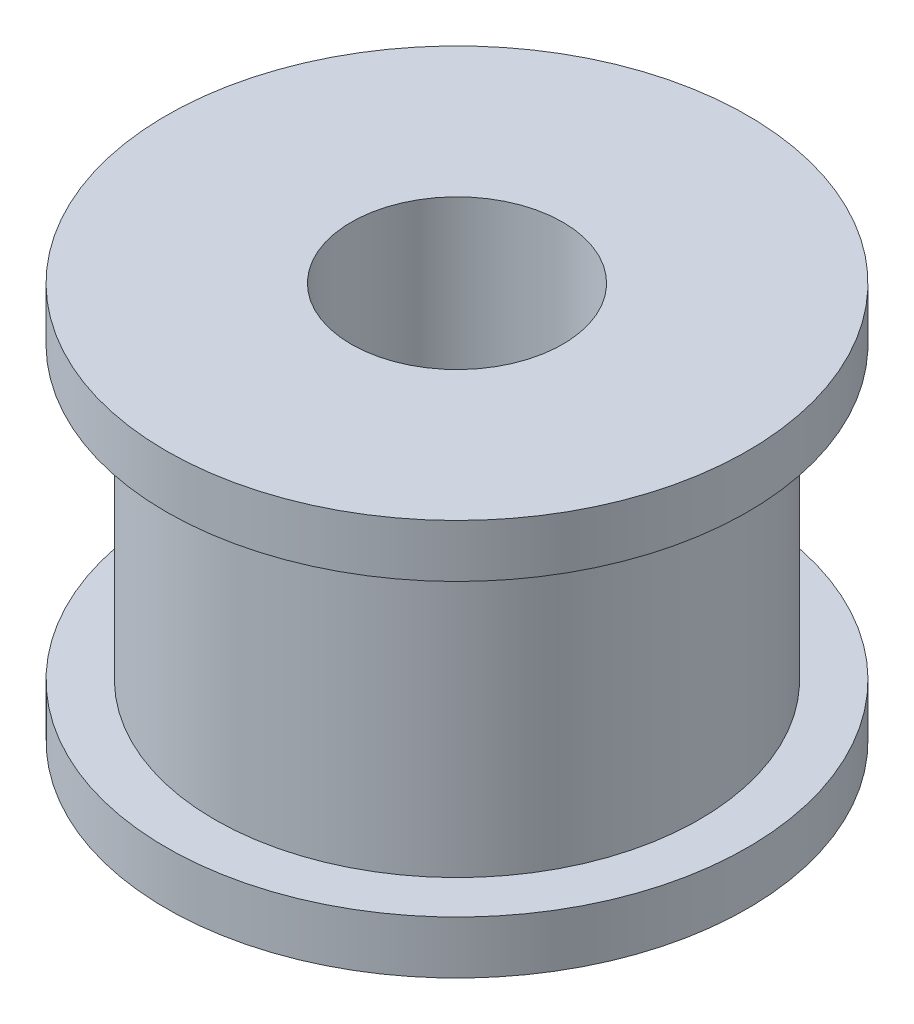
SolidWorks part; units mm, degrees
ref_plane "前视基准面" through (0, 0, 0) normal (0, 0, 1) x (1, 0, 0)
ref_plane "上视基准面" through (0, 0, 0) normal (0, 1, 0) x (1, 0, 0)
ref_plane "右视基准面" through (0, 0, 0) normal (1, 0, 0) x (0, 0, -1)
sketch "草图1" plane through (0, 0, 0) normal (0, 1, 0) x (1, 0, 0)
  circle A0 centre (0, 0) radius 9.17
  dimension "D1" = 18.34
extrude "凸台-拉伸2" add sketch "草图1" along normal blind 11
sketch "草图3" plane through (0, 11, 0) normal (0, 1, 0) x (1, 0, 0)
  circle A0 centre (0, 0) radius 11
  dimension "D1" = 22
extrude "凸台-拉伸3" add sketch "草图3" along normal blind 2
sketch "草图4" plane through (0, 0, 0) normal (0, -1, 0) x (1, 0, 0)
  circle A0 centre (0, 0) radius 11
  dimension "D1" = 22
extrude "凸台-拉伸4" add sketch "草图4" along normal blind 2
sketch "草图5" plane through (0, -2, 0) normal (0, -1, 0) x (1, 0, 0)
  circle A0 centre (0, 0) radius 4.005
  dimension "D1" = 8.01
extrude "切除-拉伸2" cut sketch "草图5" against normal through all
